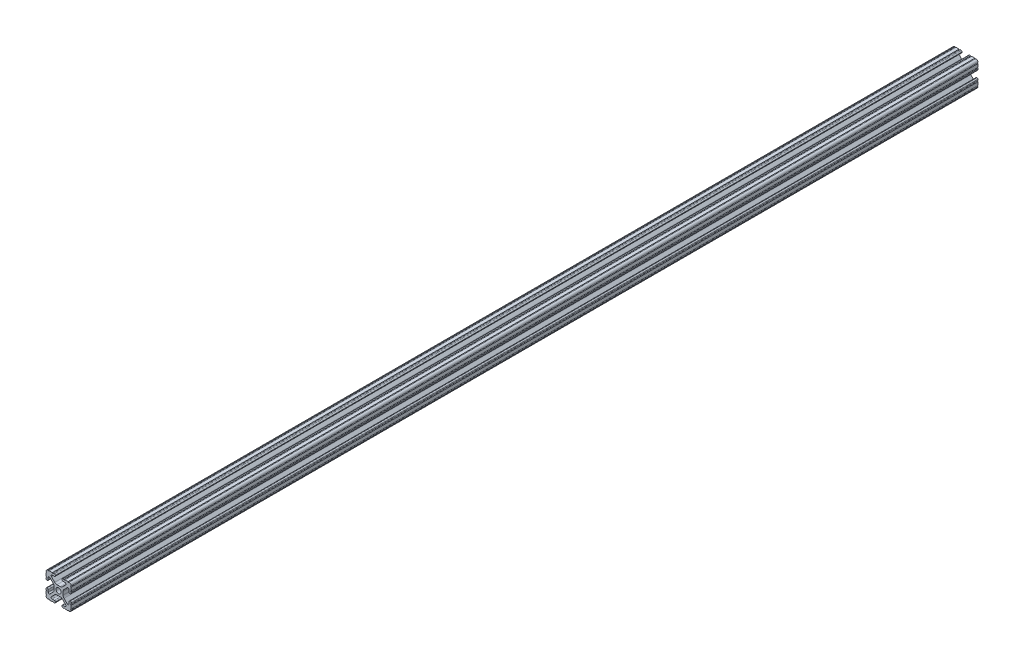
SolidWorks part; units mm, degrees
ref_plane "Front Plane" through (0, 0, 0) normal (0, 0, 1) x (1, 0, 0)
ref_plane "Top Plane" through (0, 0, 0) normal (0, 1, 0) x (1, 0, 0)
ref_plane "Right Plane" through (0, 0, 0) normal (1, 0, 0) x (0, 0, -1)
sketch "Sketch1" plane through (0, 0, 0) normal (0, 0, 1) x (1, 0, 0)
  line L88 (-7.1797, -8.6452) -> (-3.9523, -5.4237)
  line L89 (-1.7093, -4.4958) -> (1.7093, -4.4958)
  line L90 (3.9523, -5.4237) -> (7.1797, -8.6452)
  line L91 (6.4164, -10.4902) -> (4.2875, -10.4902)
  line L92 (3.2385, -11.5392) -> (3.2385, -11.651)
  line L93 (4.2875, -12.7) -> (5.3171, -12.7)
  line L94 (6.3331, -12.7) -> (9.5504, -12.7)
  line L95 (12.7, -9.5504) -> (12.7, -6.3331)
  line L96 (12.7, -5.3171) -> (12.7, -4.2875)
  line L97 (11.651, -3.2385) -> (11.5392, -3.2385)
  line L98 (10.4902, -4.2875) -> (10.4902, -6.4021)
  line L99 (8.7371, -7.1294) -> (5.441, -3.8408)
  line L100 (4.5085, -1.5932) -> (4.5085, 1.5932)
  line L101 (5.441, 3.8408) -> (8.7371, 7.1294)
  line L102 (10.4902, 6.4021) -> (10.4902, 4.2875)
  line L103 (11.5392, 3.2385) -> (11.651, 3.2385)
  line L104 (12.7, 4.2875) -> (12.7, 5.3171)
  line L105 (12.7, 6.3331) -> (12.7, 9.5504)
  line L106 (9.5504, 12.7) -> (6.3331, 12.7)
  line L107 (5.3171, 12.7) -> (4.2875, 12.7)
  line L108 (3.2385, 11.651) -> (3.2385, 11.5392)
  line L109 (4.2875, 10.4902) -> (6.4768, 10.4902)
  line L110 (7.207, 8.7244) -> (3.8983, 5.4232)
  line L111 (1.6558, 4.4958) -> (-1.6558, 4.4958)
  line L112 (-3.8983, 5.4232) -> (-7.207, 8.7244)
  line L113 (-6.4768, 10.4902) -> (-4.2875, 10.4902)
  line L114 (-3.2385, 11.5392) -> (-3.2385, 11.651)
  line L115 (-4.2875, 12.7) -> (-5.3171, 12.7)
  line L116 (-6.3331, 12.7) -> (-9.5504, 12.7)
  line L117 (-12.7, 9.5504) -> (-12.7, 6.3331)
  line L118 (-12.7, 5.3171) -> (-12.7, 4.2875)
  line L119 (-11.651, 3.2385) -> (-11.5392, 3.2385)
  line L120 (-10.4902, 4.2875) -> (-10.4902, 6.4021)
  line L121 (-8.7371, 7.1294) -> (-5.441, 3.8408)
  line L122 (-4.5085, 1.5932) -> (-4.5085, -1.5932)
  line L123 (-5.441, -3.8408) -> (-8.7371, -7.1294)
  line L124 (-10.4902, -6.4021) -> (-10.4902, -4.2875)
  line L125 (-11.5392, -3.2385) -> (-11.651, -3.2385)
  line L126 (-12.7, -4.2875) -> (-12.7, -5.3171)
  line L127 (-12.7, -6.3331) -> (-12.7, -9.5504)
  line L128 (-9.5504, -12.7) -> (-6.3331, -12.7)
  line L129 (-5.3171, -12.7) -> (-4.2875, -12.7)
  line L130 (-3.2385, -11.651) -> (-3.2385, -11.5392)
  line L131 (-4.2875, -10.4902) -> (-6.4164, -10.4902)
  circle A1 centre (0, 0) radius 2.6035
  arc A104 (-7.1797, -8.6452) -> (-6.4164, -10.4902) centre (-6.4164, -9.4098) ccw
  arc A105 (-1.7093, -4.4958) -> (-3.9523, -5.4237) centre (-1.7093, -7.6708) ccw
  arc A106 (3.9523, -5.4237) -> (1.7093, -4.4958) centre (1.7093, -7.6708) ccw
  arc A107 (6.4164, -10.4902) -> (7.1797, -8.6452) centre (6.4164, -9.4098) ccw
  arc A108 (4.2875, -10.4902) -> (3.2385, -11.5392) centre (4.2875, -11.5392) ccw
  arc A109 (3.2385, -11.651) -> (4.2875, -12.7) centre (4.2875, -11.651) ccw
  arc A110 (6.3331, -12.7) -> (5.3171, -12.7) centre (5.8251, -12.7) ccw
  arc A111 (10.5664, -12.6998) -> (9.5504, -12.7) centre (10.0584, -12.7) ccw
  arc A112 (10.5664, -12.6998) -> (12.6998, -10.5664) centre (10.5918, -10.5918) ccw
  arc A113 (12.7, -9.5504) -> (12.6998, -10.5664) centre (12.7, -10.0584) ccw
  arc A114 (12.7, -5.3171) -> (12.7, -6.3331) centre (12.7, -5.8251) ccw
  arc A115 (12.7, -4.2875) -> (11.651, -3.2385) centre (11.651, -4.2875) ccw
  arc A116 (11.5392, -3.2385) -> (10.4902, -4.2875) centre (11.5392, -4.2875) ccw
  arc A117 (8.7371, -7.1294) -> (10.4902, -6.4021) centre (9.4628, -6.4021) ccw
  arc A118 (4.5085, -1.5932) -> (5.441, -3.8408) centre (7.6835, -1.5932) ccw
  arc A119 (5.441, 3.8408) -> (4.5085, 1.5932) centre (7.6835, 1.5932) ccw
  arc A120 (10.4902, 6.4021) -> (8.7371, 7.1294) centre (9.4628, 6.4021) ccw
  arc A121 (10.4902, 4.2875) -> (11.5392, 3.2385) centre (11.5392, 4.2875) ccw
  arc A122 (11.651, 3.2385) -> (12.7, 4.2875) centre (11.651, 4.2875) ccw
  arc A123 (12.7, 6.3331) -> (12.7, 5.3171) centre (12.7, 5.8251) ccw
  arc A124 (12.6998, 10.5664) -> (12.7, 9.5504) centre (12.7, 10.0584) ccw
  arc A125 (12.6998, 10.5664) -> (10.5664, 12.6998) centre (10.5918, 10.5918) ccw
  arc A126 (9.5504, 12.7) -> (10.5664, 12.6998) centre (10.0584, 12.7) ccw
  arc A127 (5.3171, 12.7) -> (6.3331, 12.7) centre (5.8251, 12.7) ccw
  arc A128 (4.2875, 12.7) -> (3.2385, 11.651) centre (4.2875, 11.651) ccw
  arc A129 (3.2385, 11.5392) -> (4.2875, 10.4902) centre (4.2875, 11.5392) ccw
  arc A130 (7.207, 8.7244) -> (6.4768, 10.4902) centre (6.4768, 9.4563) ccw
  arc A131 (1.6558, 4.4958) -> (3.8983, 5.4232) centre (1.6558, 7.6708) ccw
  arc A132 (-3.8983, 5.4232) -> (-1.6558, 4.4958) centre (-1.6558, 7.6708) ccw
  arc A133 (-6.4768, 10.4902) -> (-7.207, 8.7244) centre (-6.4768, 9.4563) ccw
  arc A134 (-4.2875, 10.4902) -> (-3.2385, 11.5392) centre (-4.2875, 11.5392) ccw
  arc A135 (-3.2385, 11.651) -> (-4.2875, 12.7) centre (-4.2875, 11.651) ccw
  arc A136 (-6.3331, 12.7) -> (-5.3171, 12.7) centre (-5.8251, 12.7) ccw
  arc A137 (-10.5664, 12.6998) -> (-9.5504, 12.7) centre (-10.0584, 12.7) ccw
  arc A138 (-10.5664, 12.6998) -> (-12.6998, 10.5664) centre (-10.5918, 10.5918) ccw
  arc A139 (-12.7, 9.5504) -> (-12.6998, 10.5664) centre (-12.7, 10.0584) ccw
  arc A140 (-12.7, 5.3171) -> (-12.7, 6.3331) centre (-12.7, 5.8251) ccw
  arc A141 (-12.7, 4.2875) -> (-11.651, 3.2385) centre (-11.651, 4.2875) ccw
  arc A142 (-11.5392, 3.2385) -> (-10.4902, 4.2875) centre (-11.5392, 4.2875) ccw
  arc A143 (-8.7371, 7.1294) -> (-10.4902, 6.4021) centre (-9.4628, 6.4021) ccw
  arc A144 (-4.5085, 1.5932) -> (-5.441, 3.8408) centre (-7.6835, 1.5932) ccw
  arc A145 (-5.441, -3.8408) -> (-4.5085, -1.5932) centre (-7.6835, -1.5932) ccw
  arc A146 (-10.4902, -6.4021) -> (-8.7371, -7.1294) centre (-9.4628, -6.4021) ccw
  arc A147 (-10.4902, -4.2875) -> (-11.5392, -3.2385) centre (-11.5392, -4.2875) ccw
  arc A148 (-11.651, -3.2385) -> (-12.7, -4.2875) centre (-11.651, -4.2875) ccw
  arc A149 (-12.7, -6.3331) -> (-12.7, -5.3171) centre (-12.7, -5.8251) ccw
  arc A150 (-12.6998, -10.5664) -> (-12.7, -9.5504) centre (-12.7, -10.0584) ccw
  arc A151 (-12.6998, -10.5664) -> (-10.5664, -12.6998) centre (-10.5918, -10.5918) ccw
  arc A152 (-9.5504, -12.7) -> (-10.5664, -12.6998) centre (-10.0584, -12.7) ccw
  arc A153 (-5.3171, -12.7) -> (-6.3331, -12.7) centre (-5.8251, -12.7) ccw
  arc A154 (-4.2875, -12.7) -> (-3.2385, -11.651) centre (-4.2875, -11.651) ccw
  arc A155 (-3.2385, -11.5392) -> (-4.2875, -10.4902) centre (-4.2875, -11.5392) ccw
extrude "Boss-Extrude1" add sketch "Sketch1" along normal mid plane 914.4
